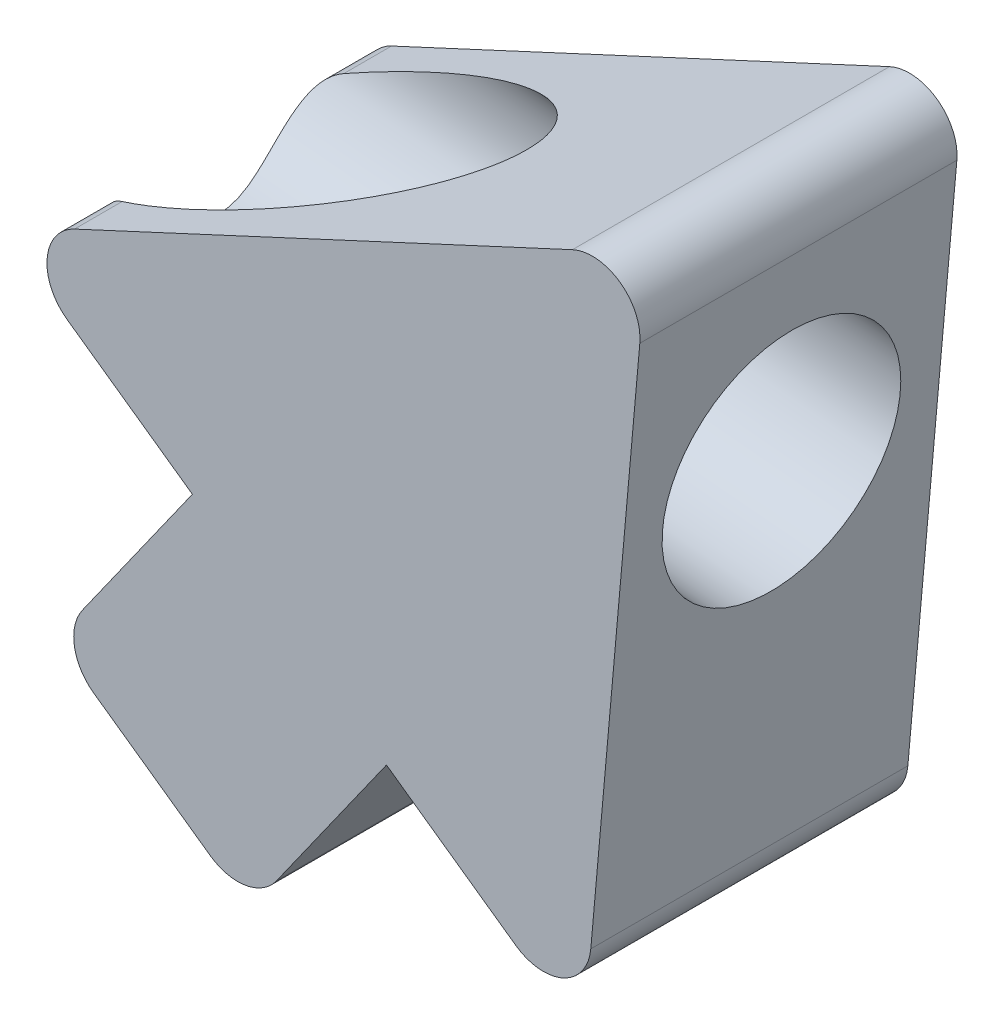
SolidWorks part; units mm, degrees
ref_plane "Front Plane" through (0, 0, 0) normal (0, 0, 1) x (1, 0, 0)
ref_plane "Top Plane" through (0, 0, 0) normal (0, 1, 0) x (1, 0, 0)
ref_plane "Right Plane" through (0, 0, 0) normal (1, 0, 0) x (0, 0, -1)
sketch "Sketch1" plane through (0, 0, 0) normal (0, 0, 1) x (1, 0, 0)
  line L0 (0, 0) -> (-10.3677, -4.812)
  line L1 (0, 0) -> (-1.0206, -11.43)
  line L2 (-10.3677, -4.812) -> (-7.286, -6.9939)
  line L3 (-7.286, -6.9939) -> (-9.4876, -10.1034)
  line L8 (-9.4876, -10.1034) -> (-6.3781, -12.305)
  line L9 (-6.3781, -12.305) -> (-4.1765, -9.1955)
  line L10 (-4.1765, -9.1955) -> (-1.0206, -11.43)
  dimension "D1" = 3.81
  dimension "D2" = 3.1559
  dimension "D3" = 11.43
  dimension "D4" = 11.43
  dimension "D5" = 3.0817
  dimension "D6" = 13.7283
  dimension "D7" = 3.81
extrude "Boss-Extrude1" add sketch "Sketch1" along normal blind 5.08
fillet "Fillet1" radius 0.762 5 edges at (-10.3677, -4.812, 2.54) (-9.4876, -10.1034, 2.54) (-6.3781, -12.305, 2.54) (-1.0206, -11.43, 2.54) (0, 0, 2.54)
sketch "Sketch2" plane through (0, 0, 0) normal (0.996, -0.0889, 0) x (0, 0, -1)
  line L0 (-5.08, -10.1504) -> (-5.08, -1.3198) construction
  line L1 (0, -0.5578) -> (-5.08, -0.5578) construction
  circle A0 centre (-2.54, -4.3678) radius 1.905
  dimension "D1" = 3.81
  dimension "D2" = 2.54
  dimension "D3" = 3.81
extrude "Cut-Extrude1" cut sketch "Sketch2" against normal through all
